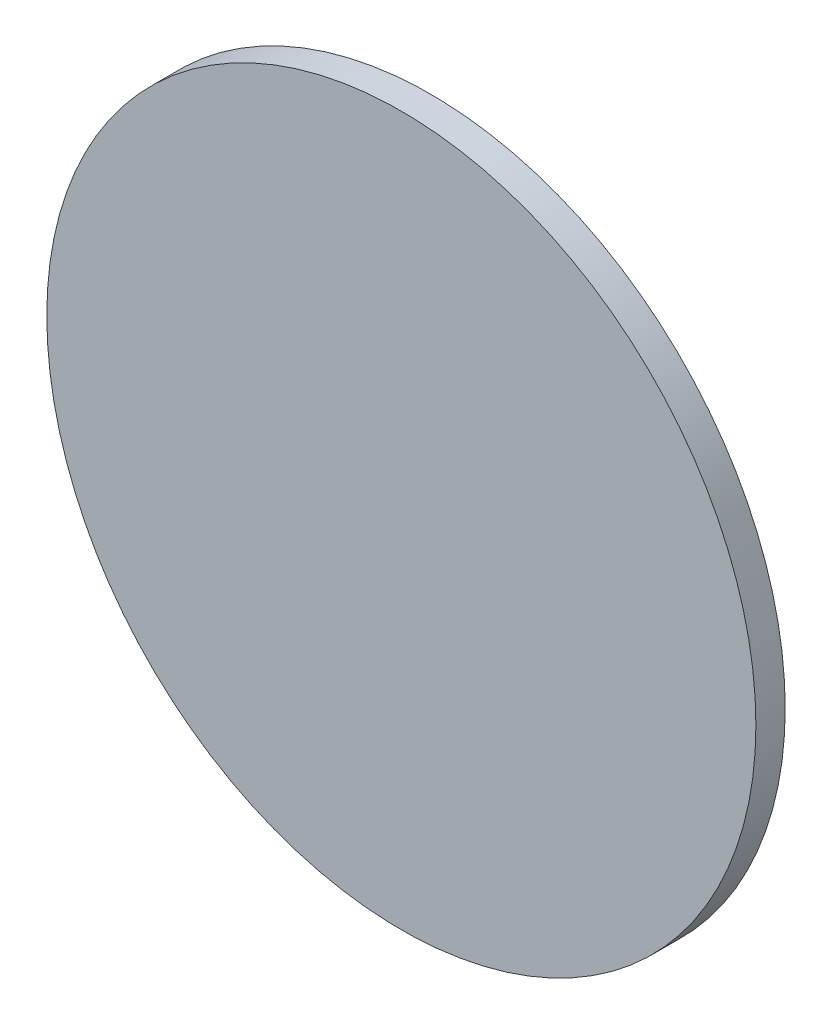
SolidWorks part; units mm, degrees
ref_plane "Front Plane" through (0, 0, 0) normal (0, 0, 1) x (1, 0, 0)
ref_plane "Top Plane" through (0, 0, 0) normal (0, 1, 0) x (1, 0, 0)
ref_plane "Right Plane" through (0, 0, 0) normal (1, 0, 0) x (0, 0, -1)
sketch "Sketch1" plane through (0, 0, 0) normal (0, 0, 1) x (1, 0, 0)
  circle A0 centre (0, 0) radius 9.525
extrude "Extrude1" add sketch "Sketch1" along normal mid plane 0.7874
